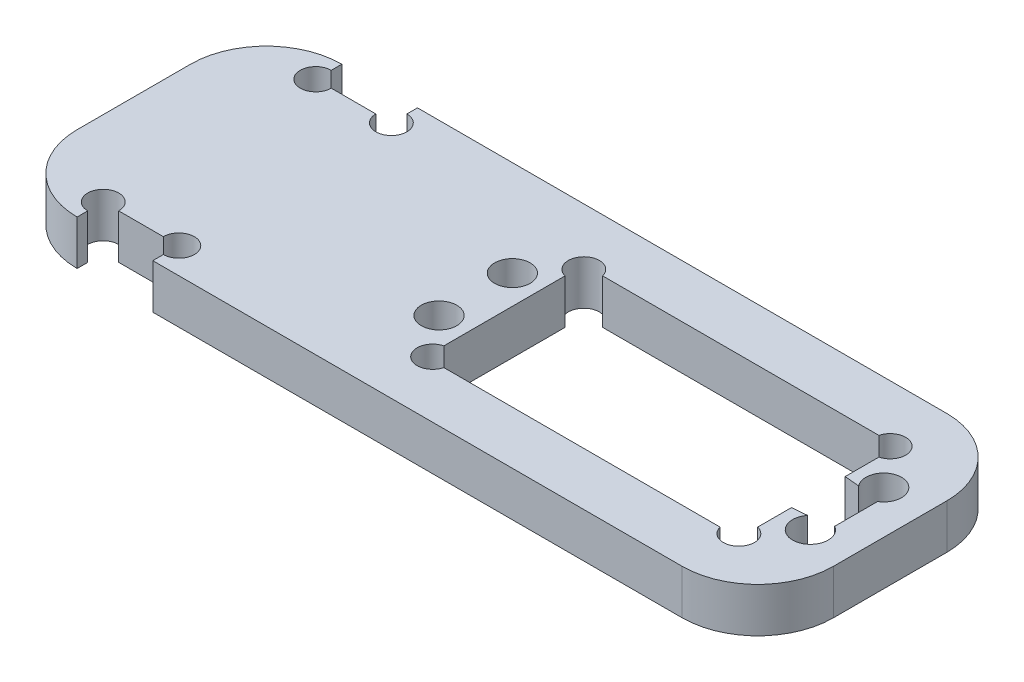
SolidWorks part; units mm, degrees
ref_plane "Front Plane" through (0, 0, 0) normal (0, 0, 1) x (1, 0, 0)
ref_plane "Top Plane" through (0, 0, 0) normal (0, 1, 0) x (1, 0, 0)
ref_plane "Right Plane" through (0, 0, 0) normal (1, 0, 0) x (0, 0, -1)
sketch "Sketch1" plane through (0, 0, 0) normal (0, 1, 0) x (1, 0, 0)
  line L0 (40, 0) -> (50, 0) construction
  line L1 (-50, -17.5) -> (50, -17.5)
  line L2 (-50, -17.5) -> (-50, 17.5)
  line L3 (-50, 17.5) -> (50, 17.5)
  line L4 (50, -17.5) -> (50, 17.5)
  line L5 (-50, -17.5) -> (50, 17.5) construction
  line L6 (-50, 17.5) -> (50, -17.5) construction
  line L11 (-4.8, 4.85) -> (44.3, 4.85) construction
  line L12 (-4.8, 4.85) -> (-4.8, -4.85) construction
  line L13 (-4.8, -4.85) -> (44.3, -4.85) construction
  line L18 (44.3, 4.85) -> (44.3, -4.85) construction
  line L19 (-4.8, 4.85) -> (44.3, -4.85) construction
  line L20 (-4.8, -4.85) -> (44.3, 4.85) construction
  line L21 (19.75, 4.85) -> (19.75, 17.5) construction
  line L22 (-0.5, 10) -> (40, 10)
  line L23 (-0.5, 10) -> (-0.5, -10)
  line L24 (-0.5, -10) -> (40, -10)
  line L25 (40, 10) -> (40, -10)
  line L26 (-0.5, 10) -> (40, -10) construction
  line L27 (-0.5, -10) -> (40, 10) construction
  circle A4 centre (-4.8, 4.85) radius 2.35
  circle A5 centre (-4.8, -4.85) radius 2.35
  circle A6 centre (44.3, -4.85) radius 2.35
  circle A7 centre (44.3, 4.85) radius 2.35
  point P0 (-4.8, 4.85)
  point P5 (-4.8, -4.85)
  point P8 (44.3, -4.85)
  point P10 (44.3, 4.85)
  point P17 (19.75, 0)
  point P27 (19.75, 0)
  dimension "D6" = 20
  dimension "D7" = 35
  dimension "D4" = 4.7
  dimension "D1" = 49.1
  dimension "D2" = 100
  dimension "D3" = 9.7
  dimension "D5" = 40.5
  dimension "D8" = 10
extrude "Boss-Extrude1" add sketch "Sketch1" along normal blind 5.9
fillet "Fillet1" radius 10 4 edges at (-50, 2.95, -17.5) (-50, 2.95, 17.5) (50, 2.95, -17.5) (50, 2.95, 17.5)
sketch "Sketch3" plane through (0, 5.9, 0) normal (0, 1, 0) x (1, 0, 0)
  line L0 (-50, 7.5) -> (-50, -7.5) construction
  line L1 (-40, 17.5) -> (-30, 17.5)
  line L2 (-40, 17.5) -> (-40, 14.05)
  line L3 (-40, 14.05) -> (-30, 14.05)
  line L4 (-30, 17.5) -> (-30, 14.05)
  line L5 (40, 17.5) -> (-40, 17.5) construction
  line L6 (0, 0) -> (-34.4726, 0) construction
  line L7 (-40, -14.05) -> (-30, -14.05)
  line L8 (-30, -17.5) -> (-30, -14.05)
  line L9 (-40, -17.5) -> (-30, -17.5)
  line L10 (-40, -17.5) -> (-40, -14.05)
  point P11 (-17.2363, 0)
  dimension "D1" = 10
  dimension "D2" = 3.45
  dimension "D3" = 10
extrude "Cut-Extrude2" cut sketch "Sketch3" against normal blind 10
sketch "Sketch4" plane through (0, 5.9, 0) normal (0, 1, 0) x (1, 0, 0)
  circle A0 centre (-30, 14.05) radius 2.05
  circle A1 centre (-40, 14.05) radius 2.05
  circle A2 centre (-40, -14.05) radius 2.05
  circle A3 centre (-30, -14.05) radius 2.05
  circle A4 centre (-0.5, 10) radius 2.05
  circle A5 centre (-0.5, -10) radius 2.05
  circle A6 centre (40, -10) radius 2.05
  circle A7 centre (40, 10) radius 2.05
  dimension "D1" = 4.1
extrude "Cut-Extrude3" cut sketch "Sketch4" against normal up to next
sketch "Sketch6" plane through (0, 5.9, 0) normal (0, 1, 0) x (1, 0, 0)
  line L0 (40, -3.1) -> (40, 3.1)
  line L1 (40, -7.95) -> (40, 7.95) construction
  line L2 (40, 3.1) -> (40, 3.6)
  line L3 (40, 3.1) -> (45.5, 3.1) construction
  line L4 (45.5, 3.1) -> (40, 3.6)
  line L5 (40, 0) -> (45.5, 0) construction
  line L6 (45.5, -3.1) -> (45.5, 3.1)
  line L7 (40, -3.1) -> (40, -3.6)
  line L8 (45.5, -3.1) -> (40, -3.6)
  dimension "D1" = 3.1
  dimension "D2" = 0.5
  dimension "D3" = 5.5
extrude "Cut-Extrude4" cut sketch "Sketch6" against normal up to next
sketch "Sketch7" plane through (0, 5.9, 0) normal (0, 1, 0) x (1, 0, 0)
  line L0 (37.95, 10) -> (1.55, 10) construction
  line L1 (-1, -10.5) -> (40.5, -10.5)
  line L2 (-1, -10.5) -> (-1, 10.5)
  line L3 (-1, 10.5) -> (40.5, 10.5)
  line L4 (40.5, -10.5) -> (40.5, 10.5)
  line L5 (-1, -10.5) -> (40.5, 10.5) construction
  line L6 (-1, 10.5) -> (40.5, -10.5) construction
  line L7 (-0.5, 7.95) -> (-0.5, -7.95) construction
  point P0 (19.75, 0)
  point P7 (19.75, 10)
  point P8 (-0.5, 0)
  dimension "D1" = 0.5
  dimension "D2" = 0.5
extrude "Cut-Extrude5" cut sketch "Sketch7" against normal up to next
equation "\"e\" = 5.9"
equation "\"D1@Boss-Extrude1\"=\"e\""
equation "\"D2@Sketch3\"= 0.5 + 0.5 * \"e\""
